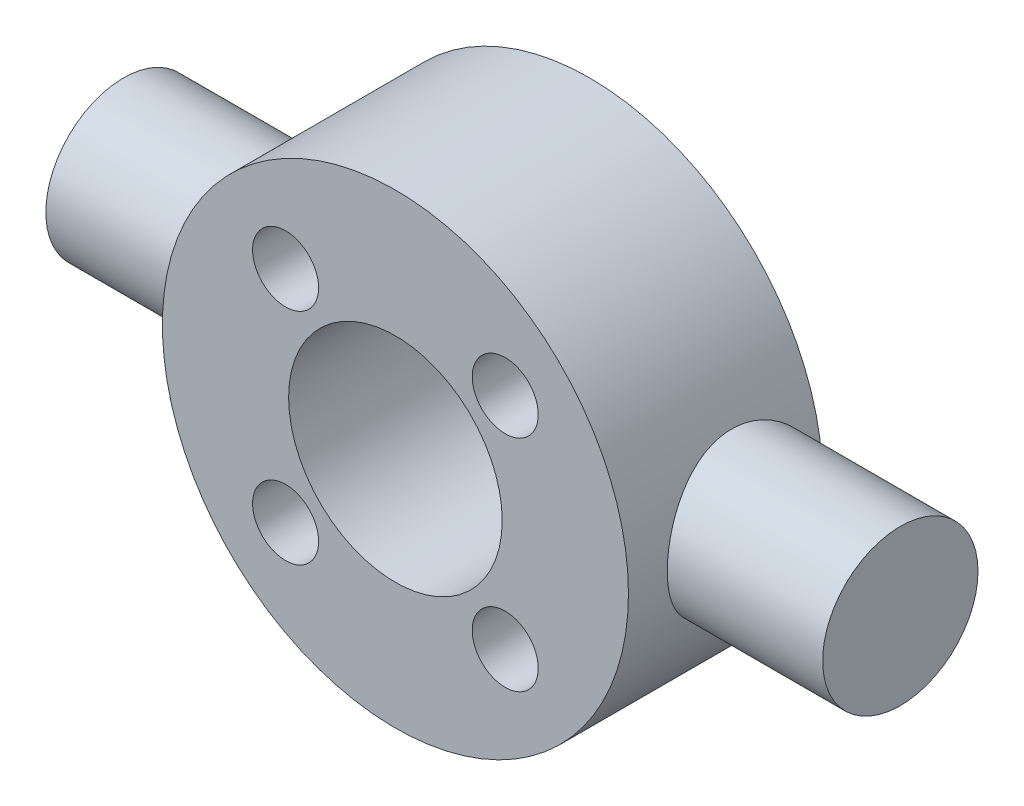
SolidWorks part; units mm, degrees
material "ABS"
ref_plane "Front" through (0, 0, 0) normal (0, 0, 1) x (1, 0, 0)
ref_plane "Top" through (0, 0, 0) normal (0, 1, 0) x (1, 0, 0)
ref_plane "Right" through (0, 0, 0) normal (1, 0, 0) x (0, 0, -1)
sketch "Croquis1" plane through (0, 0, 0) normal (0, 0, 1) x (1, 0, 0)
  line L1 (5.655, -5.655) -> (-5.655, -5.655) construction
  line L2 (5.655, -5.655) -> (5.655, 5.655) construction
  line L3 (5.655, 5.655) -> (-5.655, 5.655) construction
  line L4 (-5.655, -5.655) -> (-5.655, 5.655) construction
  line L5 (5.655, -5.655) -> (-5.655, 5.655) construction
  line L6 (5.655, 5.655) -> (-5.655, -5.655) construction
  circle A0 centre (0, 0) radius 12
  circle A2 centre (-5.655, 5.655) radius 1.7
  circle A3 centre (5.655, 5.655) radius 1.7
  circle A4 centre (5.655, -5.655) radius 1.7
  circle A5 centre (-5.655, -5.655) radius 1.7
  dimension "D1" = 24
  dimension "D3" = 3.4
  dimension "D4" = 11.31
extrude "Saliente-Extruir1" add sketch "Croquis1" along normal blind 10
sketch "Croquis2" plane through (0, 0, 0) normal (1, 0, 0) x (0, 0, -1)
  line L0 (0, -12) -> (0, 12) construction
  circle A0 centre (-4, 0) radius 4
  dimension "D1" = 8
extrude "Saliente-Extruir2" add sketch "Croquis2" along normal mid plane 40
sketch "Croquis3" plane through (0, 0, 10) normal (0, 0, 1) x (1, 0, 0)
  circle A0 centre (0, 0) radius 5.5
  dimension "D1" = 11
extrude "Cortar-Extruir1" cut sketch "Croquis3" against normal up to next
